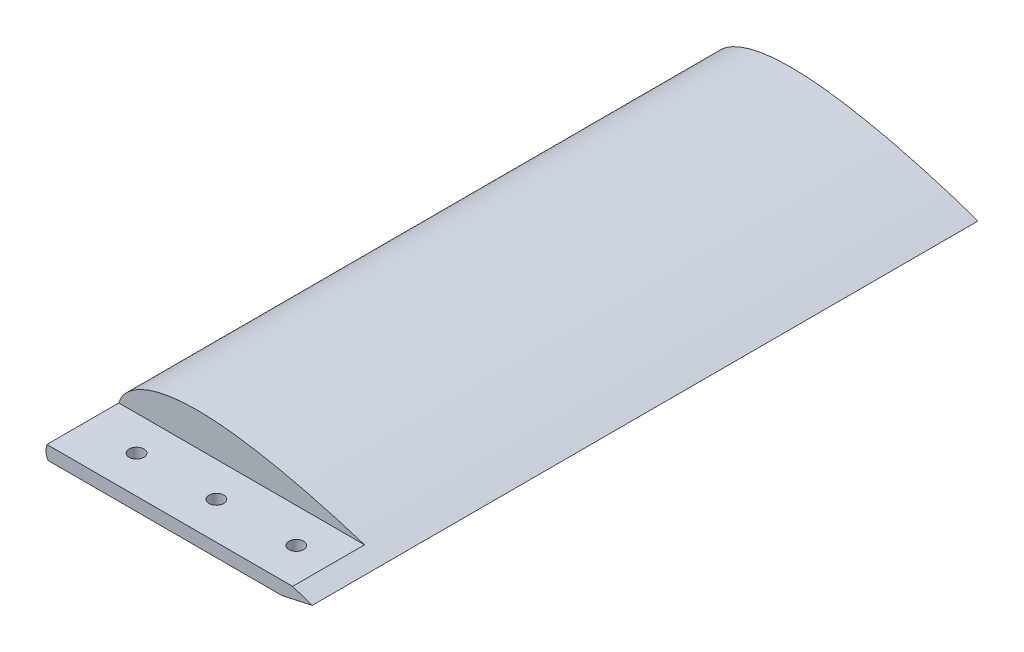
SolidWorks part; units mm, degrees
ref_plane "Front Plane" through (0, 0, 0) normal (0, 0, 1) x (1, 0, 0)
ref_plane "Top Plane" through (0, 0, 0) normal (0, 1, 0) x (1, 0, 0)
ref_plane "Right Plane" through (0, 0, 0) normal (1, 0, 0) x (0, 0, -1)
sketch "Sketch1" plane through (0, 0, 0) normal (0, 0, 1) x (1, 0, 0)
  spline S0 degree 4 poles (0, 0) (0.0009, 0.3297) (0.0295, 0.9275) (0.1439, 1.7967) (0.437, 2.9181) (0.8549, 3.9907) (1.4315, 5.0756) (2.1923, 6.1773) (3.2003, 7.33) (4.4959, 8.5106) (6.154, 9.7149) (8.2741, 10.9292) (10.957, 12.1146) (14.1477, 13.1525) (18.0405, 14.0363) (23.1343, 14.7366) (29.2357, 15.0274) (35.338, 14.8248) (41.1011, 14.3138) (46.841, 13.5968) (51.6037, 12.8505) (56.3456, 11.9834) (61.0671, 11.0139) (64.8328, 10.183) (68.5865, 9.3015) (72.3294, 8.3726) (76.0598, 7.3994) (79.3157, 6.5093) (82.096, 5.721) (84.4127, 5.0444) (86.2537, 4.4957) (88.1107, 3.9294) (89.9289, 3.3646) (91.806, 2.7666) (93.571, 2.1956) (95.5202, 1.5463) (97.1384, 1.0009) (99.1531, 0.3002) (100.3626, -0.127) (101.915, -0.6848) (103.1337, -1.1307) (104.3912, -1.5976) (105.6393, -2.0687) (106.8855, -2.5467) (108.1291, -3.0316) (109.0597, -3.4006) (109.6792, -3.6489) (109.9887, -3.7737) knots 0 0 0 0 0 0.011046 0.020082 0.029326 0.038802 0.04958 0.06121 0.074146 0.090071 0.108265 0.129827 0.155965 0.188307 0.220649 0.263591 0.328276 0.39296 0.425303 0.457645 0.522329 0.554672 0.587014 0.619356 0.651699 0.684041 0.716383 0.748725 0.764896 0.781068 0.797239 0.81341 0.829581 0.845752 0.861923 0.878094 0.894265 0.910437 0.921632 0.932827 0.944023 0.955218 0.966414 0.977609 0.988805 1 1 1 1 1 construction
  spline S1 degree 4 poles (0, 0) (0.0009, 0.3297) (0.0295, 0.9275) (0.1439, 1.7967) (0.437, 2.9181) (0.8549, 3.9907) (1.4315, 5.0756) (2.1923, 6.1773) (3.2003, 7.33) (4.4959, 8.5106) (6.154, 9.7149) (8.2741, 10.9292) (10.957, 12.1146) (14.1477, 13.1525) (18.0405, 14.0363) (23.1343, 14.7366) (29.2357, 15.0274) (35.338, 14.8248) (41.1011, 14.3138) (46.841, 13.5968) (51.6037, 12.8505) (56.3456, 11.9834) (61.0671, 11.0139) (64.8328, 10.183) (68.5865, 9.3015) (72.3294, 8.3726) (76.0598, 7.3994) (79.3157, 6.5093) (82.096, 5.721) (84.4127, 5.0444) (86.2537, 4.4957) (88.1107, 3.9294) (89.9289, 3.3646) (91.806, 2.7666) (93.571, 2.1956) (95.5202, 1.5463) (97.1383, 1.0009) (98.7751, 0.4317) (99.5867, 0.1465) (100.0002, 0) knots 0 0 0 0 0 0.011046 0.020082 0.029326 0.038802 0.04958 0.06121 0.074146 0.090071 0.108265 0.129827 0.155965 0.188307 0.220649 0.263591 0.328276 0.39296 0.425303 0.457645 0.522329 0.554672 0.587014 0.619356 0.651699 0.684041 0.716383 0.748725 0.764896 0.781068 0.797239 0.81341 0.829581 0.845752 0.861923 0.878094 0.894265 0.910434 0.910434 0.910434 0.910434 0.910434
  spline S2 degree 4 poles (0, 0) (0.0003, -0.1693) (0.016, -0.4614) (0.0775, -0.8851) (0.2333, -1.4356) (0.4512, -1.9609) (0.763, -2.5157) (1.1968, -3.1118) (1.8009, -3.7667) (2.6459, -4.4954) (3.845, -5.3152) (5.5202, -6.2106) (7.8905, -7.1807) (10.9471, -8.0963) (15.4296, -9.0396) (21.208, -9.73) (27.9775, -10.0275) (35.6486, -9.8891) (42.3469, -9.4657) (48.0748, -8.9399) (53.7915, -8.3061) (59.4968, -7.5766) (65.1885, -6.7461) (70.8667, -5.8302) (75.5899, -5.0142) (79.3624, -4.3307) (82.6596, -3.7058) (85.4801, -3.1515) (87.5962, -2.7233) (89.0005, -2.4341) (90.1811, -2.1872) (91.104, -1.9926) (92.3051, -1.7354) (93.6554, -1.4439) (95.3898, -1.0596) (97.1027, -0.6748) (99.4365, -0.1347) (101.1191, 0.2637) (103.9947, 0.9599) (105.7889, 1.4169) (107.9207, 1.9617) (109.0082, 2.2534) (109.6995, 2.4359) (109.9984, 2.5166) knots 0 0 0 0 0 0.005887 0.010193 0.014867 0.019889 0.025655 0.032315 0.040498 0.050865 0.064448 0.082823 0.106556 0.139954 0.175459 0.242256 0.309053 0.375849 0.442646 0.476045 0.509443 0.57624 0.643037 0.676435 0.709833 0.743232 0.77663 0.793329 0.810028 0.818378 0.826728 0.835077 0.843427 0.860126 0.876825 0.893524 0.910224 0.932668 0.955112 0.977556 0.988778 1 1 1 1 1 construction
  spline S3 degree 4 poles (0, 0) (0.0003, -0.1693) (0.016, -0.4614) (0.0775, -0.8851) (0.2333, -1.4356) (0.4512, -1.9609) (0.763, -2.5157) (1.1968, -3.1118) (1.8009, -3.7667) (2.6459, -4.4954) (3.845, -5.3152) (5.5202, -6.2106) (7.8905, -7.1807) (10.9471, -8.0963) (15.4296, -9.0396) (21.208, -9.73) (27.9775, -10.0275) (35.6486, -9.8891) (42.3469, -9.4657) (48.0748, -8.9399) (53.7915, -8.3061) (59.4968, -7.5766) (65.1885, -6.7461) (70.8667, -5.8302) (75.5899, -5.0142) (79.3624, -4.3307) (82.6596, -3.7058) (85.4801, -3.1515) (87.5962, -2.7233) (89.0005, -2.4341) (90.1811, -2.1872) (91.104, -1.9926) (92.3051, -1.7354) (93.6554, -1.4439) (95.3898, -1.0596) (97.1027, -0.6748) (98.7145, -0.3018) (99.5756, -0.1002) (100.0002, 0) knots 0 0 0 0 0 0.005887 0.010193 0.014867 0.019889 0.025655 0.032315 0.040498 0.050865 0.064448 0.082823 0.106556 0.139954 0.175459 0.242256 0.309053 0.375849 0.442646 0.476045 0.509443 0.57624 0.643037 0.676435 0.709833 0.743232 0.77663 0.793329 0.810028 0.818378 0.826728 0.835077 0.843427 0.860126 0.876825 0.893524 0.910224 0.910224 0.910224 0.910224 0.910224
sketch "Sketch2" plane through (0, 0, 0) normal (0, 1, 0) x (1, 0, 0)
  line L1 (0, 0) -> (0, -250) construction
  line L2 (0, -250) -> (50, -500) construction
  spline S0 degree 2 poles (0, 0) (0, -250) (50, -500) knots 0 0 0 1 1 1
  dimension "D1" = 250
  dimension "D2" = 250
  dimension "D3" = 50
ref_plane "Plane2" through (0, 0, 500) normal (0, 0, 1) x (1, 0, 0)
sketch "Sketch5" plane through (0, 0, 500) normal (0, 0, 1) x (1, 0, 0)
  spline S0 degree 4 poles (44.9961, 0) (44.997, 0.3297) (45.0257, 0.9275) (45.14, 1.7967) (45.4332, 2.9181) (45.851, 3.9907) (46.4276, 5.0756) (47.1884, 6.1773) (48.1965, 7.33) (49.4921, 8.5106) (51.1502, 9.7149) (53.2702, 10.9292) (55.9531, 12.1146) (59.1438, 13.1525) (63.0366, 14.0363) (68.1305, 14.7366) (74.2318, 15.0274) (80.3341, 14.8248) (86.0972, 14.3138) (91.8371, 13.5968) (96.5999, 12.8505) (101.3417, 11.9834) (106.0633, 11.0139) (109.8289, 10.183) (113.5826, 9.3015) (117.3256, 8.3726) (121.0559, 7.3994) (124.3119, 6.5093) (127.0921, 5.721) (129.4089, 5.0444) (131.2499, 4.4957) (133.1069, 3.9294) (134.9251, 3.3646) (136.8022, 2.7666) (138.5672, 2.1956) (140.5163, 1.5463) (142.1345, 1.0009) (144.1492, 0.3002) (145.3587, -0.127) (146.9111, -0.6848) (148.1299, -1.1307) (149.3874, -1.5976) (150.6354, -2.0687) (151.8817, -2.5467) (153.1253, -3.0316) (154.0559, -3.4006) (154.6753, -3.6489) (154.9848, -3.7737) knots 0 0 0 0 0 0.011046 0.020082 0.029326 0.038802 0.04958 0.06121 0.074146 0.090071 0.108265 0.129827 0.155965 0.188307 0.220649 0.263591 0.328276 0.39296 0.425303 0.457645 0.522329 0.554672 0.587014 0.619356 0.651699 0.684041 0.716383 0.748725 0.764896 0.781068 0.797239 0.81341 0.829581 0.845752 0.861923 0.878094 0.894265 0.910437 0.921632 0.932827 0.944023 0.955218 0.966414 0.977609 0.988805 1 1 1 1 1 construction
  spline S1 degree 4 poles (44.9961, 0) (44.997, 0.3297) (45.0257, 0.9275) (45.14, 1.7967) (45.4332, 2.9181) (45.851, 3.9907) (46.4276, 5.0756) (47.1884, 6.1773) (48.1965, 7.33) (49.4921, 8.5106) (51.1502, 9.7149) (53.2702, 10.9292) (55.9531, 12.1146) (59.1438, 13.1525) (63.0366, 14.0363) (68.1305, 14.7366) (74.2318, 15.0274) (80.3341, 14.8248) (86.0972, 14.3138) (91.8371, 13.5968) (96.5999, 12.8505) (101.3417, 11.9834) (106.0633, 11.0139) (109.8289, 10.183) (113.5826, 9.3015) (117.3256, 8.3726) (121.0559, 7.3994) (124.3119, 6.5093) (127.0921, 5.721) (129.4089, 5.0444) (131.2499, 4.4957) (133.1069, 3.9294) (134.9251, 3.3646) (136.8022, 2.7666) (138.5672, 2.1956) (140.5163, 1.5463) (142.1344, 1.0009) (143.7713, 0.4317) (144.5828, 0.1465) (144.9964, 0) knots 0 0 0 0 0 0.011046 0.020082 0.029326 0.038802 0.04958 0.06121 0.074146 0.090071 0.108265 0.129827 0.155965 0.188307 0.220649 0.263591 0.328276 0.39296 0.425303 0.457645 0.522329 0.554672 0.587014 0.619356 0.651699 0.684041 0.716383 0.748725 0.764896 0.781068 0.797239 0.81341 0.829581 0.845752 0.861923 0.878094 0.894265 0.910434 0.910434 0.910434 0.910434 0.910434 construction
  spline S2 degree 4 poles (44.9961, 0) (44.9964, -0.1693) (45.0121, -0.4614) (45.0736, -0.8851) (45.2294, -1.4356) (45.4474, -1.9609) (45.7592, -2.5157) (46.193, -3.1118) (46.7971, -3.7667) (47.642, -4.4954) (48.8411, -5.3152) (50.5163, -6.2106) (52.8866, -7.1807) (55.9432, -8.0963) (60.4257, -9.0396) (66.2041, -9.73) (72.9737, -10.0275) (80.6447, -9.8891) (87.343, -9.4657) (93.071, -8.9399) (98.7876, -8.3061) (104.493, -7.5766) (110.1846, -6.7461) (115.8628, -5.8302) (120.586, -5.0142) (124.3586, -4.3307) (127.6557, -3.7058) (130.4762, -3.1515) (132.5924, -2.7233) (133.9966, -2.4341) (135.1772, -2.1872) (136.1002, -1.9926) (137.3012, -1.7354) (138.6515, -1.4439) (140.3859, -1.0596) (142.0988, -0.6748) (144.4327, -0.1347) (146.1152, 0.2637) (148.9908, 0.9599) (150.7851, 1.4169) (152.9168, 1.9617) (154.0043, 2.2534) (154.6957, 2.4359) (154.9945, 2.5166) knots 0 0 0 0 0 0.005887 0.010193 0.014867 0.019889 0.025655 0.032315 0.040498 0.050865 0.064448 0.082823 0.106556 0.139954 0.175459 0.242256 0.309053 0.375849 0.442646 0.476045 0.509443 0.57624 0.643037 0.676435 0.709833 0.743232 0.77663 0.793329 0.810028 0.818378 0.826728 0.835077 0.843427 0.860126 0.876825 0.893524 0.910224 0.932668 0.955112 0.977556 0.988778 1 1 1 1 1 construction
  spline S3 degree 4 poles (44.9961, 0) (44.9964, -0.1693) (45.0121, -0.4614) (45.0736, -0.8851) (45.2294, -1.4356) (45.4474, -1.9609) (45.7592, -2.5157) (46.193, -3.1118) (46.7971, -3.7667) (47.642, -4.4954) (48.8411, -5.3152) (50.5163, -6.2106) (52.8866, -7.1807) (55.9432, -8.0963) (60.4257, -9.0396) (66.2041, -9.73) (72.9737, -10.0275) (80.6447, -9.8891) (87.343, -9.4657) (93.071, -8.9399) (98.7876, -8.3061) (104.493, -7.5766) (110.1846, -6.7461) (115.8628, -5.8302) (120.586, -5.0142) (124.3586, -4.3307) (127.6557, -3.7058) (130.4762, -3.1515) (132.5924, -2.7233) (133.9966, -2.4341) (135.1772, -2.1872) (136.1002, -1.9926) (137.3012, -1.7354) (138.6515, -1.4439) (140.3859, -1.0596) (142.0988, -0.6748) (143.7106, -0.3018) (144.5718, -0.1002) (144.9964, 0) knots 0 0 0 0 0 0.005887 0.010193 0.014867 0.019889 0.025655 0.032315 0.040498 0.050865 0.064448 0.082823 0.106556 0.139954 0.175459 0.242256 0.309053 0.375849 0.442646 0.476045 0.509443 0.57624 0.643037 0.676435 0.709833 0.743232 0.77663 0.793329 0.810028 0.818378 0.826728 0.835077 0.843427 0.860126 0.876825 0.893524 0.910224 0.910224 0.910224 0.910224 0.910224 construction
  spline S4 degree 1 poles (50, 0.1659) (125.4884, 0.9751) knots 0 0 1 1 construction
  spline S5 degree 1 poles (50, 0.1659) (125.4884, 0.9751) knots 0 0 1 1 construction
  spline S6 degree 3 poles (50, 0.1659) (50.0179, 0.6032) (50.1757, 1.4567) (50.8242, 2.7316) (51.9666, 4.0552) (54.0561, 5.71) (57.4359, 7.406) (62.0985, 8.7726) (67.0831, 9.581) (73.966, 10.0492) (82.8075, 9.7192) (93.5157, 8.3656) (107.7971, 5.6881) (118.4649, 2.9873) (125.4884, 0.9751) knots 0.003107 0.003107 0.003107 0.003107 0.026472 0.049837 0.073202 0.096568 0.143298 0.190028 0.236758 0.283489 0.376949 0.47041 0.56387 0.750791 0.750791 0.750791 0.750791
  spline S7 degree 3 poles (125.4884, 0.9751) (118.8048, -0.2943) (108.7202, -1.9955) (95.2701, -3.722) (85.1977, -4.6498) (76.8507, -4.9962) (70.2537, -4.8947) (65.3724, -4.5831) (61.4032, -4.0773) (58.338, -3.4825) (56.1227, -2.928) (54.0329, -2.2507) (52.4618, -1.576) (51.3904, -0.9852) (50.7151, -0.5321) (50.3053, -0.1828) (50.0857, 0.053) (50.0309, 0.1225) (50, 0.1659) knots 0.025551 0.025551 0.025551 0.025551 0.205368 0.295277 0.385186 0.475094 0.520049 0.565003 0.609957 0.632435 0.654912 0.677389 0.699866 0.711105 0.722343 0.733582 0.739201 0.74482 0.74482 0.74482 0.74482
  spline S8 degree 1 poles (57.6356, 1.8665) (100.2923, 1.9767) knots 0 0 1 1 construction
  spline S9 degree 1 poles (57.6356, 1.8665) (100.2923, 1.9767) knots 0 0 1 1 construction
  spline S10 degree 3 poles (57.6356, 1.8665) (57.9231, 2.0151) (58.4925, 2.2874) (59.782, 2.82) (61.5543, 3.4029) (63.8869, 3.9672) (67.1912, 4.5347) (71.5938, 4.9175) (77.127, 4.9346) (82.8116, 4.5908) (88.5912, 3.9528) (94.4204, 3.0772) (98.3432, 2.3598) (100.2923, 1.9767) knots 0.118651 0.118651 0.118651 0.118651 0.131754 0.144858 0.171065 0.197272 0.223479 0.275893 0.328307 0.380721 0.433135 0.485549 0.537964 0.537964 0.537964 0.537964
  spline S11 degree 3 poles (100.2923, 1.9767) (98.4159, 1.7345) (94.6502, 1.2813) (87.1702, 0.537) (79.7557, 0.0753) (72.5111, 0.0364) (68.0926, 0.2319) (64.6731, 0.551) (62.1863, 0.8819) (60.2071, 1.2401) (58.6967, 1.5822) (57.9917, 1.7662) (57.6356, 1.8665) knots 0.116889 0.116889 0.116889 0.116889 0.167972 0.219056 0.321223 0.372307 0.42339 0.448932 0.474474 0.500016 0.512787 0.525558 0.525558 0.525558 0.525558
  dimension "D1" = 5
  dimension "D3" = 50
  dimension "D2" = 10
sketch "Sketch6" plane through (0, 0, 0) normal (0, 0, 1) x (1, 0, 0)
  spline S0 degree 4 poles (0, 0) (0.0009, 0.3297) (0.0295, 0.9275) (0.1439, 1.7967) (0.437, 2.9181) (0.8549, 3.9907) (1.4315, 5.0756) (2.1923, 6.1773) (3.2003, 7.33) (4.4959, 8.5106) (6.154, 9.7149) (8.2741, 10.9292) (10.957, 12.1146) (14.1477, 13.1525) (18.0405, 14.0363) (23.1343, 14.7366) (29.2357, 15.0274) (35.338, 14.8248) (41.1011, 14.3138) (46.841, 13.5968) (51.6037, 12.8505) (56.3456, 11.9834) (61.0671, 11.0139) (64.8328, 10.183) (68.5865, 9.3015) (72.3294, 8.3726) (76.0598, 7.3994) (79.3157, 6.5093) (82.096, 5.721) (84.4127, 5.0444) (86.2537, 4.4957) (88.1107, 3.9294) (89.9289, 3.3646) (91.806, 2.7666) (93.571, 2.1956) (95.5202, 1.5463) (97.1384, 1.0009) (99.1531, 0.3002) (100.3626, -0.127) (101.915, -0.6848) (103.1337, -1.1307) (104.3912, -1.5976) (105.6393, -2.0687) (106.8855, -2.5467) (108.1291, -3.0316) (109.0597, -3.4006) (109.6792, -3.6489) (109.9887, -3.7737) knots 0 0 0 0 0 0.011046 0.020082 0.029326 0.038802 0.04958 0.06121 0.074146 0.090071 0.108265 0.129827 0.155965 0.188307 0.220649 0.263591 0.328276 0.39296 0.425303 0.457645 0.522329 0.554672 0.587014 0.619356 0.651699 0.684041 0.716383 0.748725 0.764896 0.781068 0.797239 0.81341 0.829581 0.845752 0.861923 0.878094 0.894265 0.910437 0.921632 0.932827 0.944023 0.955218 0.966414 0.977609 0.988805 1 1 1 1 1 construction
  spline S1 degree 4 poles (0, 0) (0.0009, 0.3297) (0.0295, 0.9275) (0.1439, 1.7967) (0.437, 2.9181) (0.8549, 3.9907) (1.4315, 5.0756) (2.1923, 6.1773) (3.2003, 7.33) (4.4959, 8.5106) (6.154, 9.7149) (8.2741, 10.9292) (10.957, 12.1146) (14.1477, 13.1525) (18.0405, 14.0363) (23.1343, 14.7366) (29.2357, 15.0274) (35.338, 14.8248) (41.1011, 14.3138) (46.841, 13.5968) (51.6037, 12.8505) (56.3456, 11.9834) (61.0671, 11.0139) (64.8328, 10.183) (68.5865, 9.3015) (72.3294, 8.3726) (76.0598, 7.3994) (79.3157, 6.5093) (82.096, 5.721) (84.4127, 5.0444) (86.2537, 4.4957) (88.1107, 3.9294) (89.9289, 3.3646) (91.806, 2.7666) (93.571, 2.1956) (95.5202, 1.5463) (97.1383, 1.0009) (98.7751, 0.4317) (99.5867, 0.1465) (100.0002, 0) knots 0 0 0 0 0 0.011046 0.020082 0.029326 0.038802 0.04958 0.06121 0.074146 0.090071 0.108265 0.129827 0.155965 0.188307 0.220649 0.263591 0.328276 0.39296 0.425303 0.457645 0.522329 0.554672 0.587014 0.619356 0.651699 0.684041 0.716383 0.748725 0.764896 0.781068 0.797239 0.81341 0.829581 0.845752 0.861923 0.878094 0.894265 0.910434 0.910434 0.910434 0.910434 0.910434 construction
  spline S2 degree 4 poles (0, 0) (0.0003, -0.1693) (0.016, -0.4614) (0.0775, -0.8851) (0.2333, -1.4356) (0.4512, -1.9609) (0.763, -2.5157) (1.1968, -3.1118) (1.8009, -3.7667) (2.6459, -4.4954) (3.845, -5.3152) (5.5202, -6.2106) (7.8905, -7.1807) (10.9471, -8.0963) (15.4296, -9.0396) (21.208, -9.73) (27.9775, -10.0275) (35.6486, -9.8891) (42.3469, -9.4657) (48.0748, -8.9399) (53.7915, -8.3061) (59.4968, -7.5766) (65.1885, -6.7461) (70.8667, -5.8302) (75.5899, -5.0142) (79.3624, -4.3307) (82.6596, -3.7058) (85.4801, -3.1515) (87.5962, -2.7233) (89.0005, -2.4341) (90.1811, -2.1872) (91.104, -1.9926) (92.3051, -1.7354) (93.6554, -1.4439) (95.3898, -1.0596) (97.1027, -0.6748) (99.4365, -0.1347) (101.1191, 0.2637) (103.9947, 0.9599) (105.7889, 1.4169) (107.9207, 1.9617) (109.0082, 2.2534) (109.6995, 2.4359) (109.9984, 2.5166) knots 0 0 0 0 0 0.005887 0.010193 0.014867 0.019889 0.025655 0.032315 0.040498 0.050865 0.064448 0.082823 0.106556 0.139954 0.175459 0.242256 0.309053 0.375849 0.442646 0.476045 0.509443 0.57624 0.643037 0.676435 0.709833 0.743232 0.77663 0.793329 0.810028 0.818378 0.826728 0.835077 0.843427 0.860126 0.876825 0.893524 0.910224 0.932668 0.955112 0.977556 0.988778 1 1 1 1 1 construction
  spline S3 degree 4 poles (0, 0) (0.0003, -0.1693) (0.016, -0.4614) (0.0775, -0.8851) (0.2333, -1.4356) (0.4512, -1.9609) (0.763, -2.5157) (1.1968, -3.1118) (1.8009, -3.7667) (2.6459, -4.4954) (3.845, -5.3152) (5.5202, -6.2106) (7.8905, -7.1807) (10.9471, -8.0963) (15.4296, -9.0396) (21.208, -9.73) (27.9775, -10.0275) (35.6486, -9.8891) (42.3469, -9.4657) (48.0748, -8.9399) (53.7915, -8.3061) (59.4968, -7.5766) (65.1885, -6.7461) (70.8667, -5.8302) (75.5899, -5.0142) (79.3624, -4.3307) (82.6596, -3.7058) (85.4801, -3.1515) (87.5962, -2.7233) (89.0005, -2.4341) (90.1811, -2.1872) (91.104, -1.9926) (92.3051, -1.7354) (93.6554, -1.4439) (95.3898, -1.0596) (97.1027, -0.6748) (98.7145, -0.3018) (99.5756, -0.1002) (100.0002, 0) knots 0 0 0 0 0 0.005887 0.010193 0.014867 0.019889 0.025655 0.032315 0.040498 0.050865 0.064448 0.082823 0.106556 0.139954 0.175459 0.242256 0.309053 0.375849 0.442646 0.476045 0.509443 0.57624 0.643037 0.676435 0.709833 0.743232 0.77663 0.793329 0.810028 0.818378 0.826728 0.835077 0.843427 0.860126 0.876825 0.893524 0.910224 0.910224 0.910224 0.910224 0.910224 construction
  spline S4 degree 1 poles (5.0039, 0.1659) (80.4922, 0.9751) knots 0 0 1 1 construction
  spline S5 degree 1 poles (5.0039, 0.1659) (80.4922, 0.9751) knots 0 0 1 1 construction
  spline S6 degree 3 poles (5.0039, 0.1659) (5.0218, 0.6032) (5.1796, 1.4567) (5.8281, 2.7316) (6.9704, 4.0552) (9.0599, 5.71) (12.4398, 7.406) (17.1024, 8.7726) (22.0869, 9.581) (28.9699, 10.0492) (37.8114, 9.7192) (48.5196, 8.3656) (62.801, 5.6881) (73.4687, 2.9873) (80.4922, 0.9751) knots 0.003107 0.003107 0.003107 0.003107 0.026472 0.049837 0.073202 0.096568 0.143298 0.190028 0.236758 0.283489 0.376949 0.47041 0.56387 0.750791 0.750791 0.750791 0.750791
  spline S7 degree 3 poles (80.4922, 0.9751) (73.8087, -0.2943) (63.7241, -1.9955) (50.274, -3.722) (40.2016, -4.6498) (31.8546, -4.9962) (25.2576, -4.8947) (20.3763, -4.5831) (16.407, -4.0773) (13.3418, -3.4825) (11.1266, -2.928) (9.0368, -2.2507) (7.4657, -1.576) (6.3942, -0.9852) (5.719, -0.5321) (5.3091, -0.1828) (5.0896, 0.053) (5.0347, 0.1225) (5.0039, 0.1659) knots 0.025551 0.025551 0.025551 0.025551 0.205368 0.295277 0.385186 0.475094 0.520049 0.565003 0.609957 0.632435 0.654912 0.677389 0.699866 0.711105 0.722343 0.733582 0.739201 0.74482 0.74482 0.74482 0.74482
  dimension "D1" = 5
extrude "Boss-Extrude1" add sketch "Sketch1" along normal mid plane 250
extrude "Cut-Extrude1" cut sketch "Sketch6" against normal blind 110 and the other way blind 90
sketch "Sketch9" plane through (0, 0, 125) normal (0, 0, 1) x (1, 0, 0)
  line L1 (0, 2.5) -> (100, 2.5)
  line L2 (0, 2.5) -> (0, -2.5)
  line L3 (0, -2.5) -> (100, -2.5)
  line L4 (100, 2.5) -> (100, -2.5)
  point P4 (0, 0)
  dimension "D1" = 100
  dimension "D2" = 5
extrude "Cut-Extrude2" cut sketch "Sketch9" against normal blind 27 flip side to cut contours L1 L4 L3 L2
hole_wizard "M5 Clearance Hole1" positions "Sketch13" profile "Sketch14" hole size "M5" standard "ISO" end condition through all
sketch "Sketch13" plane through (0, 2.5, 0) normal (0, 1, 0) x (1, 0, 0)
  line L7 (92.6266, -98) -> (0.3394, -98) construction
  line L11 (100.0001, -98) -> (100.0002, 125) construction
  point P0 (20, -111)
  point P4 (80, -111)
  point P6 (-19.7717, -210)
  point P30 (50, -111)
  dimension "D1" = 30
  dimension "D2" = 50
  dimension "D3" = 13
  dimension "D5" = 30
sketch "Sketch14" plane through (20, 2.5, 111) normal (1, 0, 0) x (0, 0, 1)
  line L0 (0, 0) -> (0, 12.5275)
  line L1 (0, 12.5275) -> (2.75, 12.5275)
  line L2 (2.75, 12.5275) -> (2.75, 0)
  line L5 (2.75, 0) -> (0, 0)
  line L11 (0, -6.35) -> (0, 107.95) construction
  dimension "Thru Hole Dia." = 5.5
  dimension "Thru Hole Depth" = 12.5275
sketch "Sketch15" plane through (0, 0, -125) normal (0, 0, -1) x (-1, 0, 0)
  line L1 (-42.5, -5) -> (-27.5, -5)
  line L2 (-42.5, -5) -> (-42.5, 5)
  line L3 (-42.5, 5) -> (-27.5, 5)
  line L4 (-27.5, -5) -> (-27.5, 5)
  line L5 (-47.5, 5) -> (-62.5, 5)
  line L6 (-47.5, 5) -> (-47.5, -5)
  line L7 (-47.5, -5) -> (-62.5, -5)
  line L8 (-62.5, 5) -> (-62.5, -5)
  line L9 (-22.5, 5) -> (-7.5, 5)
  line L10 (-22.5, 5) -> (-22.5, -5)
  line L11 (-22.5, -5) -> (-7.5, -5)
  line L12 (-7.5, 5) -> (-7.5, -5)
  point P4 (-7.5, 0)
  point P5 (-27.5, 0)
  point P12 (-47.5, 0)
  point P17 (-35, 5)
  dimension "D1" = 35
  dimension "D2" = 15
  dimension "D3" = 10
  dimension "D4" = 15
  dimension "D5" = 10
  dimension "D6" = 5
  dimension "D7" = 15
  dimension "D8" = 10
  dimension "D9" = 5
extrude "Cut-Extrude3" cut sketch "Sketch15" against normal blind 10
sketch "Sketch17" plane through (0, 0, 98) normal (0, 0, 1) x (1, 0, 0)
  line L0 (15.5085, 6.2) -> (17.5085, 6.2)
  line L1 (17.5085, 6.2) -> (16.0085, 4.7)
  line L2 (16.0085, 4.7) -> (17.5085, 4.7)
  line L3 (15.5085, 6.2) -> (15.5085, 6)
  line L4 (15.5085, 6) -> (17.0085, 6)
  line L5 (17.0085, 6) -> (15.5085, 4.5)
  line L6 (15.5085, 4.5) -> (17.5085, 4.5)
  line L7 (17.5085, 4.5) -> (17.5085, 4.7)
  line L9 (13.3424, 6.3) -> (13.3424, 5.5)
  line L10 (13.3424, 6.5) -> (13.0424, 6.5)
  line L11 (13.0424, 6.5) -> (13.0424, 4.1)
  line L12 (13.0424, 4.1) -> (13.3424, 4.1)
  line L13 (13.3424, 5.3) -> (14.0352, 4.1)
  line L14 (14.0352, 4.1) -> (14.3816, 4.1)
  line L15 (14.3816, 4.1) -> (13.6424, 5.3804)
  line L16 (13.3424, 5.3) -> (13.3424, 4.1)
  line L17 (0.7723, -2.5) -> (88.6781, -2.5) construction
  arc A0 (13.3424, 6.5) -> (13.6424, 5.3804) centre (13.3424, 5.9) cw
  arc A1 (13.3424, 6.3) -> (13.3424, 5.5) centre (13.3424, 5.9) cw
  point P26 (13.1924, 4.1)
  dimension "D8" = 0.6
  dimension "D9" = 0.4
  dimension "D1" = 2
  dimension "D2" = 45
  dimension "D3" = 45
  dimension "D4" = 0.5
  dimension "D5" = 0.2
  dimension "D6" = 0.5
  dimension "D7" = 8.7
  dimension "D10" = 0.3
  dimension "D11" = 30
  dimension "D12" = 0.2
  dimension "D13" = 0
  dimension "D14" = 0.3
